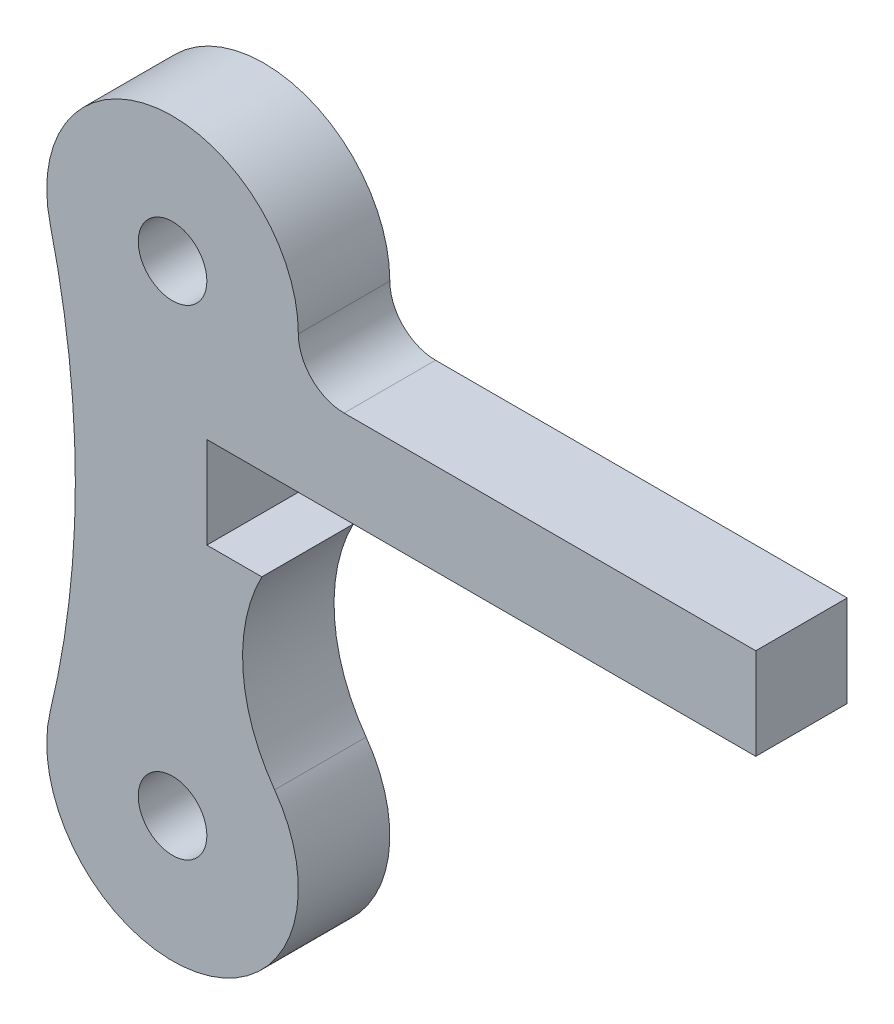
SolidWorks part; units mm, degrees
ref_plane "Front Plane" through (0, 0, 0) normal (0, 0, 1) x (1, 0, 0)
ref_plane "Top Plane" through (0, 0, 0) normal (0, 1, 0) x (1, 0, 0)
ref_plane "Right Plane" through (0, 0, 0) normal (1, 0, 0) x (0, 0, -1)
sketch "Sketch1" plane through (0, 0, 0) normal (0, 0, 1) x (1, 0, 0)
  line L0 (0, 0) -> (0, -21) construction
  line L1 (7.5, -2) -> (25.5, -2)
  line L2 (10.5, -6) -> (25.5, -6)
  line L3 (25.5, -2) -> (25.5, -6)
  circle A0 centre (0, 0) radius 1.5
  circle A1 centre (0, 0) radius 5.5
  circle A2 centre (0, -21) radius 1.5
  circle A3 centre (0, -21) radius 5.5
  arc A4 (-5.3463, -1.2912) -> (-5.3463, -19.7088) centre (-43.475, -10.5) cw
  arc A5 (5.5, 0) -> (7.5, -2) centre (7.5, 0) ccw
  arc A6 (4.4632, -17.7861) -> (10.5, -6) centre (10.5, -13.439) cw
  point P7 (-4.25, -10.5)
  dimension "D1" = 4
  dimension "D2" = 3
  dimension "D4" = 0
  dimension "D7" = 4.25
  dimension "D8" = 15
  dimension "D3" = 21
  dimension "D5" = 4
  dimension "D6" = 20
  dimension "D9" = 15
extrude "Boss-Extrude1" add sketch "Sketch1" along normal blind 4
sketch "Sketch2" plane through (0, 0, 4) normal (0, 0, 1) x (1, 0, 0)
  line L0 (25.5, -2) -> (25.5, -6) construction
  line L1 (1.5, -6) -> (25.5, -6)
  line L2 (1.5, -6) -> (1.5, -10)
  line L3 (1.5, -10) -> (25.5, -10)
  line L4 (25.5, -6) -> (25.5, -10)
  line L5 (10.5, -6) -> (25.5, -6) construction
  circle A0 centre (0, 0) radius 1.5 construction
extrude "Cut-Extrude1" cut sketch "Sketch2" against normal blind 10
